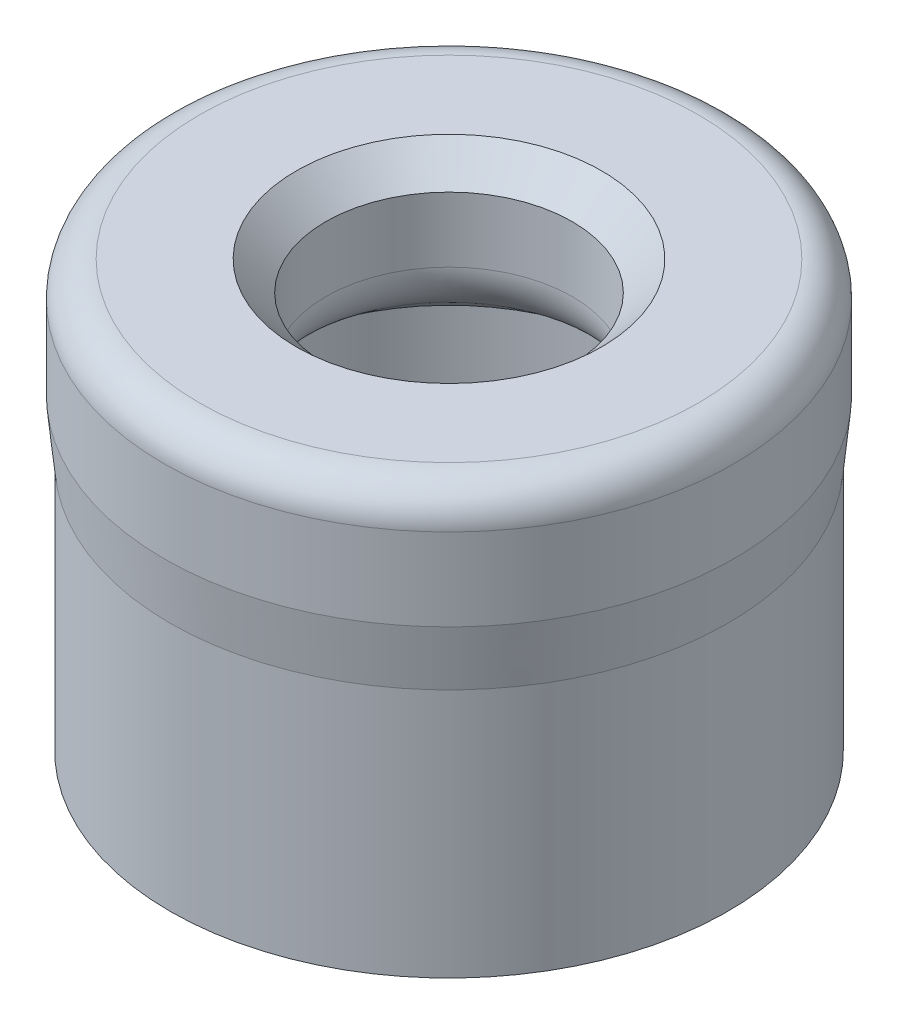
SolidWorks part; units mm, degrees
material "ABS"
ref_plane "Alzado" through (0, 0, 0) normal (0, 0, 1) x (1, 0, 0)
ref_plane "Planta" through (0, 0, 0) normal (0, 1, 0) x (1, 0, 0)
ref_plane "Vista lateral" through (0, 0, 0) normal (1, 0, 0) x (0, 0, -1)
sketch "Croquis1" plane through (0, 0, 0) normal (0, 1, 0) x (1, 0, 0)
  circle A0 centre (0, 0) radius 3.275
  circle A1 centre (0, 0) radius 4.75
  dimension "D1" = 9.5
  dimension "D2" = 6.55
extrude "Saliente-Extruir1" add sketch "Croquis1" along normal blind 4.25
sketch "Croquis2" plane through (0, 0, 0) normal (0, 0, 1) x (1, 0, 0)
  line L0 (-4.75, 4.25) -> (-4.85, 5.25)
  line L1 (-4.85, 5.25) -> (-2.1, 5.25)
  line L2 (-2.1, 5.25) -> (-2.1, 5.15)
  line L3 (-2.1, 5.15) -> (-3.275, 4.25)
  line L4 (4.75, 4.25) -> (-4.75, 4.25) construction
  line L5 (0, 0) -> (0, 6.8987) construction
  line L6 (-4.75, 4.25) -> (-3.275, 4.25)
  dimension "D1" = 4.2
  dimension "D2" = 0.1
  dimension "D3" = 2.75
  dimension "D4" = 1
revolve "Revolución1" add sketch "Croquis2" angle 360 about L5
sketch "Croquis3" plane through (0, 5.25, 0) normal (0, 1, 0) x (1, 0, 0)
  circle A0 centre (0, 0) radius 2.1
  circle A1 centre (0, 0) radius 4.85
  circle A2 centre (0, 0) radius 4.85 construction
  circle A3 centre (0, 0) radius 2.1 construction
extrude "Saliente-Extruir2" add sketch "Croquis3" along normal blind 2
fillet "Redondeo1" radius 0.6 1 edges at (0, 7.25, 4.85)
sketch "Croquis4" plane through (0, 7.25, 0) normal (0, 1, 0) x (1, 0, 0)
  circle A0 centre (0, 0) radius 3.2
  dimension "D1" = 6.4
fillet "Redondeo2" radius 1 1 edges at (0, 5.15, -2.1)
chamfer "Chaflán1" distance 0.7 angle 45 1 edges at (0, 0, 3.275)
chamfer "Chaflán2" distance 0.5 angle 45 1 edges at (0, 7.25, 2.1)
